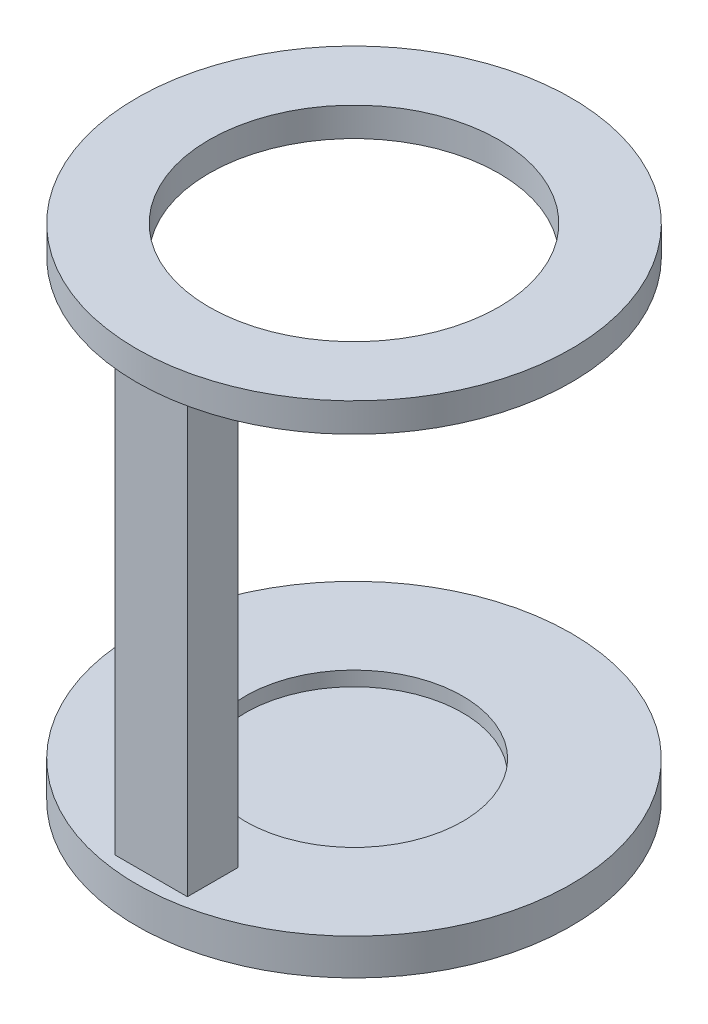
SolidWorks part; units mm, degrees
ref_plane "Front Plane" through (0, 0, 0) normal (0, 0, 1) x (1, 0, 0)
ref_plane "Top Plane" through (0, 0, 0) normal (0, 1, 0) x (1, 0, 0)
ref_plane "Right Plane" through (0, 0, 0) normal (1, 0, 0) x (0, 0, -1)
sketch "Sketch1" plane through (0, 0, 0) normal (0, 1, 0) x (1, 0, 0)
  circle A0 centre (0, 0) radius 25.4
  circle A1 centre (0, 0) radius 38.1
  dimension "D1" = 76.2
  dimension "D2" = 50.8
extrude "Boss-Extrude1" add sketch "Sketch1" along normal blind 5.08
sketch "Sketch4" plane through (0, 0, 0) normal (0, -1, 0) x (1, 0, 0)
  line L0 (0, -43.5707) -> (0, 40.0401) construction
  line L1 (-6.35, 35.56) -> (6.35, 35.56)
  line L2 (-6.35, 35.56) -> (-6.35, 26.67)
  line L3 (-6.35, 26.67) -> (6.35, 26.67)
  line L4 (6.35, 35.56) -> (6.35, 26.67)
  dimension "D1" = 12.7
  dimension "D2" = 8.89
  dimension "D3" = 26.67
extrude "Boss-Extrude3" add sketch "Sketch4" along normal blind 76.2
sketch "Sketch5" plane through (0, -76.2, 0) normal (0, -1, 0) x (1, 0, 0)
  circle A0 centre (0, 0) radius 38.1
extrude "Boss-Extrude4" add sketch "Sketch5" along normal blind 6.35
sketch "Sketch6" plane through (0, -76.2, 0) normal (0, 1, 0) x (1, 0, 0)
  circle A0 centre (0, 0) radius 19.05
  dimension "D1" = 38.1
extrude "Cut-Extrude1" cut sketch "Sketch6" against normal blind 2.54
